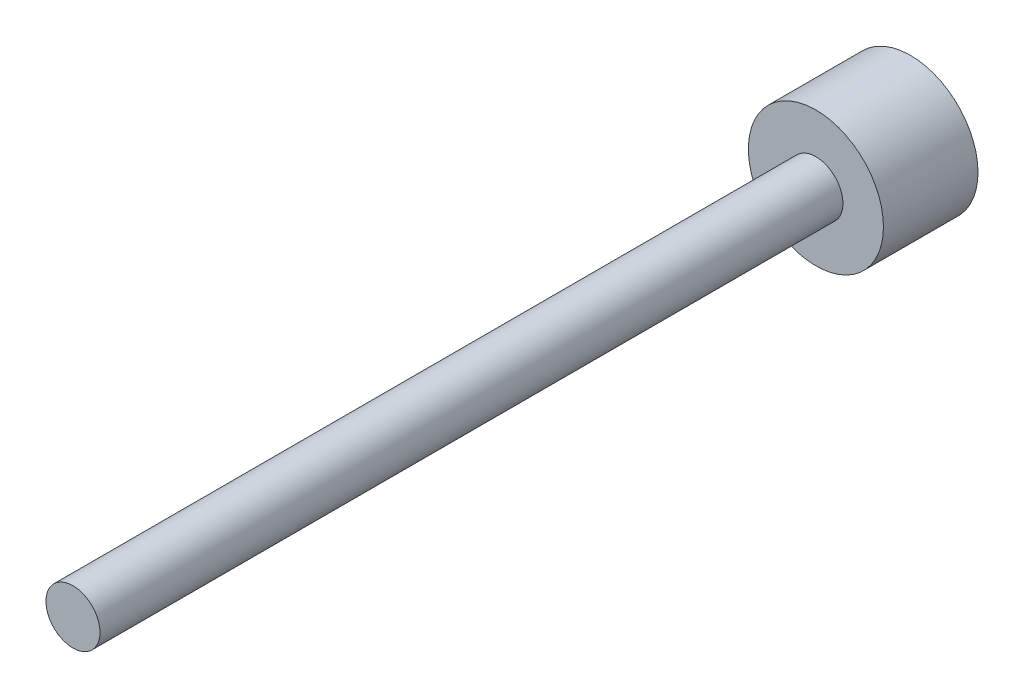
SolidWorks part; units mm, degrees
ref_plane "Front Plane" through (0, 0, 0) normal (0, 0, 1) x (1, 0, 0)
ref_plane "Top Plane" through (0, 0, 0) normal (0, 1, 0) x (1, 0, 0)
ref_plane "Right Plane" through (0, 0, 0) normal (1, 0, 0) x (0, 0, -1)
sketch "Sketch1" plane through (0, 0, 0) normal (0, 0, 1) x (1, 0, 0)
  circle A0 centre (0, 0) radius 6.35
  dimension "D1" = 12.7
extrude "Boss-Extrude1" add sketch "Sketch1" along normal blind 8.89
sketch "Sketch2" plane through (0, 0, 8.89) normal (0, 0, 1) x (1, 0, 0)
  circle A0 centre (0, 0) radius 2.54
  dimension "D1" = 5.08
extrude "Boss-Extrude2" add sketch "Sketch2" along normal blind 69.85
